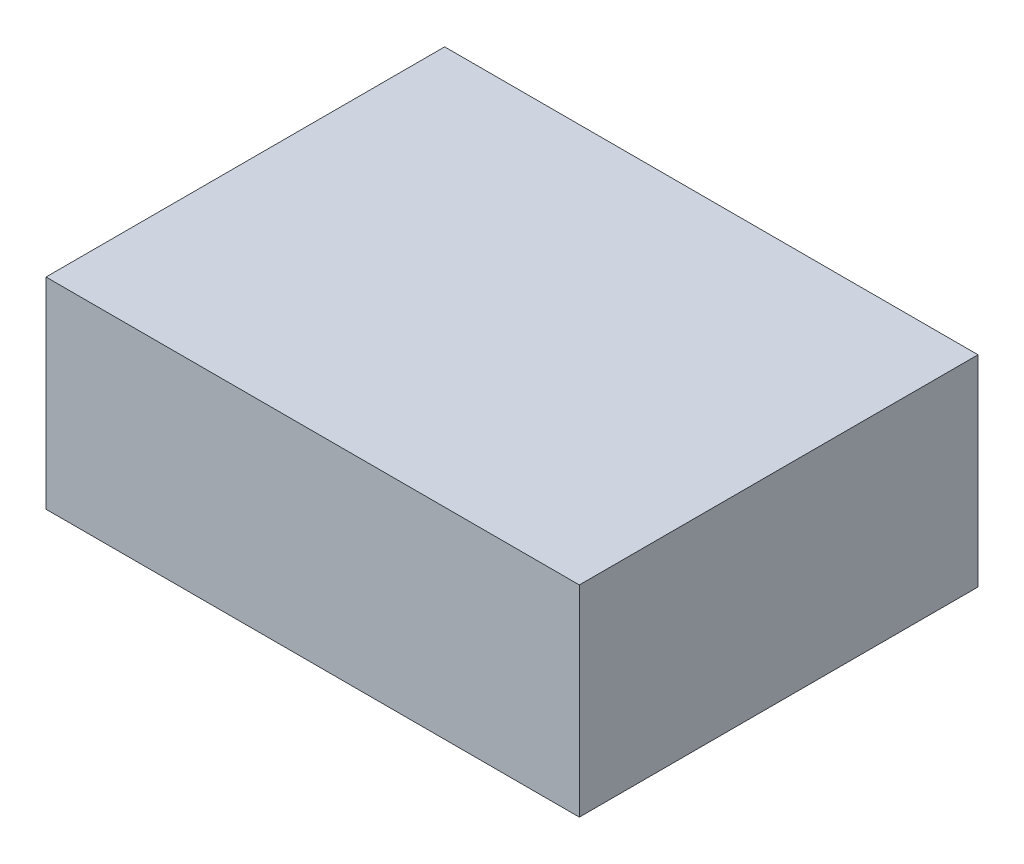
SolidWorks part; units mm, degrees
ref_plane "Front Plane" through (0, 0, 0) normal (0, 0, 1) x (1, 0, 0)
ref_plane "Top Plane" through (0, 0, 0) normal (0, 1, 0) x (1, 0, 0)
ref_plane "Right Plane" through (0, 0, 0) normal (1, 0, 0) x (0, 0, -1)
sketch "Sketch1" plane through (0, 0, 0) normal (0, 1, 0) x (1, 0, 0)
  line L1 (0, 0) -> (7.5438, 0)
  line L2 (0, 0) -> (0, 5.6388)
  line L3 (0, 5.6388) -> (7.5438, 5.6388)
  line L4 (7.5438, 0) -> (7.5438, 5.6388)
  dimension "D1" = 7.5438
  dimension "D2" = 5.6388
extrude "Boss-Extrude1" add sketch "Sketch1" along normal blind 2.8448
